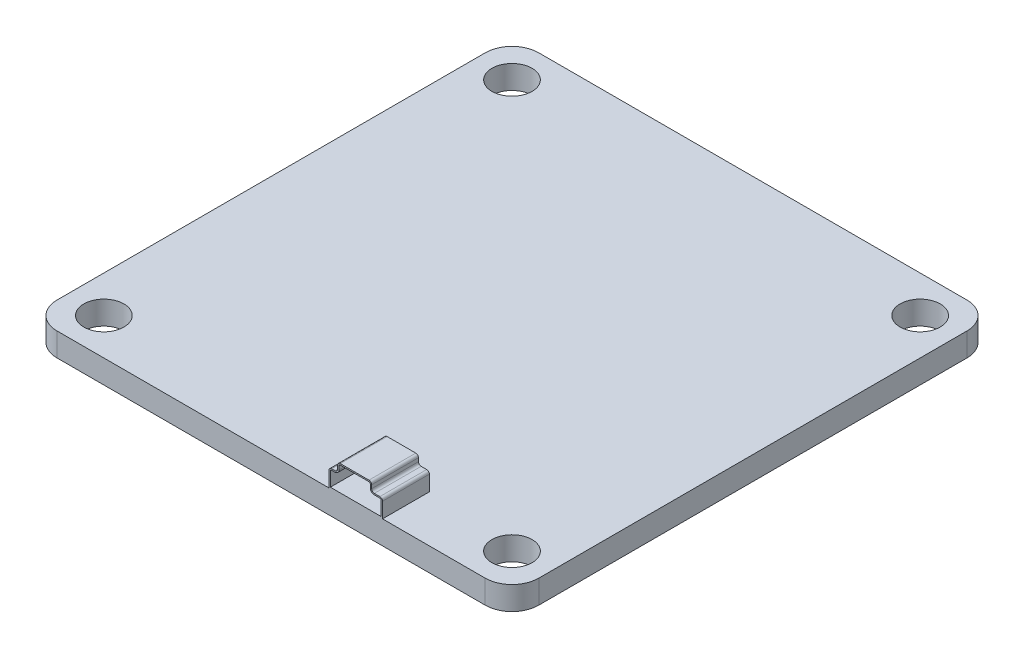
SolidWorks part; units mm, degrees
ref_plane "Front Plane" through (0, 0, 0) normal (0, 0, 1) x (1, 0, 0)
ref_plane "Top Plane" through (0, 0, 0) normal (0, 1, 0) x (1, 0, 0)
ref_plane "Right Plane" through (0, 0, 0) normal (1, 0, 0) x (0, 0, -1)
sketch "Sketch1" plane through (0, 0, 0) normal (0, 1, 0) x (1, 0, 0)
  line L1 (16, -18) -> (-16, -18)
  line L2 (18, -16) -> (18, 16)
  line L3 (16, 18) -> (-16, 18)
  line L4 (-18, -16) -> (-18, 16)
  line L5 (18, -18) -> (-18, 18) construction
  line L6 (18, 18) -> (-18, -18) construction
  line L7 (15.25, -15.25) -> (-15.25, -15.25) construction
  line L8 (15.25, -15.25) -> (15.25, 15.25) construction
  line L9 (15.25, 15.25) -> (-15.25, 15.25) construction
  line L10 (-15.25, -15.25) -> (-15.25, 15.25) construction
  line L11 (15.25, -15.25) -> (-15.25, 15.25) construction
  line L12 (15.25, 15.25) -> (-15.25, -15.25) construction
  circle A0 centre (-15.25, 15.25) radius 1.5
  circle A1 centre (15.25, 15.25) radius 1.5
  circle A2 centre (15.25, -15.25) radius 1.5
  circle A3 centre (-15.25, -15.25) radius 1.5
  arc A4 (-16, -18) -> (-18, -16) centre (-16, -16) cw
  arc A5 (16, -18) -> (18, -16) centre (16, -16) ccw
  arc A6 (18, 16) -> (16, 18) centre (16, 16) ccw
  arc A7 (-16, 18) -> (-18, 16) centre (-16, 16) ccw
  point P0 (0, 0)
  point P6 (0, 0)
  dimension "D4" = 3
  dimension "D5" = 2
  dimension "D1" = 36
  dimension "D2" = 36
  dimension "D3" = 30.5
extrude "Boss-Extrude1" add sketch "Sketch1" along normal blind 1.75
sketch "Sketch2" plane through (0, 0, 18) normal (0, 0, 1) x (1, 0, 0)
  line L0 (-16, 1.75) -> (16, 1.75) construction
  line L1 (4.3259, 1.75) -> (8.3259, 1.75)
  line L2 (4.3259, 1.75) -> (4.3259, 2.8932)
  line L3 (5.1702, 3.75) -> (7.3106, 3.75)
  line L4 (8.3259, 1.75) -> (8.3259, 2.8932)
  line L5 (4.9702, 3.55) -> (4.9702, 3.2932)
  line L6 (4.7702, 3.0932) -> (4.5259, 3.0932)
  line L7 (7.5106, 3.55) -> (7.5106, 3.2932)
  line L8 (7.7106, 3.0932) -> (8.1259, 3.0932)
  line L9 (4.4259, 1.85) -> (8.2259, 1.85)
  line L10 (8.2259, 1.85) -> (8.2259, 2.8932)
  line L11 (7.7106, 2.9932) -> (8.1259, 2.9932)
  line L12 (7.4106, 3.55) -> (7.4106, 3.2932)
  line L13 (5.1702, 3.65) -> (7.3106, 3.65)
  line L14 (5.0702, 3.55) -> (5.0702, 3.2932)
  line L15 (4.7702, 2.9932) -> (4.5259, 2.9932)
  line L16 (4.4259, 1.85) -> (4.4259, 2.8932)
  arc A0 (8.1259, 3.0932) -> (8.3259, 2.8932) centre (8.1259, 2.8932) cw
  arc A1 (7.5106, 3.2932) -> (7.7106, 3.0932) centre (7.7106, 3.2932) ccw
  arc A2 (7.5106, 3.55) -> (7.3106, 3.75) centre (7.3106, 3.55) ccw
  arc A3 (4.9702, 3.55) -> (5.1702, 3.75) centre (5.1702, 3.55) cw
  arc A4 (4.9702, 3.2932) -> (4.7702, 3.0932) centre (4.7702, 3.2932) cw
  arc A5 (4.5259, 3.0932) -> (4.3259, 2.8932) centre (4.5259, 2.8932) ccw
  arc A6 (8.1259, 2.9932) -> (8.2259, 2.8932) centre (8.1259, 2.8932) cw
  arc A7 (7.4106, 3.2932) -> (7.7106, 2.9932) centre (7.7106, 3.2932) ccw
  arc A8 (7.4106, 3.55) -> (7.3106, 3.65) centre (7.3106, 3.55) ccw
  arc A9 (5.0702, 3.55) -> (5.1702, 3.65) centre (5.1702, 3.55) cw
  arc A10 (5.0702, 3.2932) -> (4.7702, 2.9932) centre (4.7702, 3.2932) cw
  arc A11 (4.5259, 2.9932) -> (4.4259, 2.8932) centre (4.5259, 2.8932) ccw
  dimension "D1" = 0.2
  dimension "D2" = 0.1
extrude "Boss-Extrude2" add sketch "Sketch2" against normal blind 3
sketch "Sketch3" plane through (0, 0, 15) normal (0, 0, -1) x (-1, 0, 0)
  line L8 (-4.3259, 1.75) -> (-4.3259, 2.8932)
  line L9 (-4.5259, 3.0932) -> (-4.7702, 3.0932)
  line L10 (-4.9702, 3.2932) -> (-4.9702, 3.55)
  line L11 (-5.1702, 3.75) -> (-7.3106, 3.75)
  line L12 (-7.5106, 3.55) -> (-7.5106, 3.2932)
  line L13 (-7.7106, 3.0932) -> (-8.1259, 3.0932)
  line L14 (-8.3259, 2.8932) -> (-8.3259, 1.75)
  line L15 (-8.3259, 1.75) -> (-4.3259, 1.75)
  line L16 (-4.3259, 1.75) -> (-4.3259, 2.8932)
  line L17 (-4.5259, 3.0932) -> (-4.7702, 3.0932)
  line L18 (-4.9702, 3.2932) -> (-4.9702, 3.55)
  line L19 (-5.1702, 3.75) -> (-7.3106, 3.75)
  line L20 (-7.5106, 3.55) -> (-7.5106, 3.2932)
  line L21 (-7.7106, 3.0932) -> (-8.1259, 3.0932)
  line L22 (-8.3259, 2.8932) -> (-8.3259, 1.75)
  line L23 (-8.3259, 1.75) -> (-4.3259, 1.75)
  arc A6 (-4.3259, 2.8932) -> (-4.5259, 3.0932) centre (-4.5259, 2.8932) ccw
  arc A7 (-4.9702, 3.2932) -> (-4.7702, 3.0932) centre (-4.7702, 3.2932) ccw
  arc A8 (-4.9702, 3.55) -> (-5.1702, 3.75) centre (-5.1702, 3.55) ccw
  arc A9 (-7.3106, 3.75) -> (-7.5106, 3.55) centre (-7.3106, 3.55) ccw
  arc A10 (-7.7106, 3.0932) -> (-7.5106, 3.2932) centre (-7.7106, 3.2932) ccw
  arc A11 (-8.1259, 3.0932) -> (-8.3259, 2.8932) centre (-8.1259, 2.8932) ccw
  arc A12 (-4.3259, 2.8932) -> (-4.5259, 3.0932) centre (-4.5259, 2.8932) ccw
  arc A13 (-4.9702, 3.2932) -> (-4.7702, 3.0932) centre (-4.7702, 3.2932) ccw
  arc A14 (-4.9702, 3.55) -> (-5.1702, 3.75) centre (-5.1702, 3.55) ccw
  arc A15 (-7.3106, 3.75) -> (-7.5106, 3.55) centre (-7.3106, 3.55) ccw
  arc A16 (-7.7106, 3.0932) -> (-7.5106, 3.2932) centre (-7.7106, 3.2932) ccw
  arc A17 (-8.1259, 3.0932) -> (-8.3259, 2.8932) centre (-8.1259, 2.8932) ccw
  dimension "D1" = 0
extrude "Boss-Extrude3" add sketch "Sketch3" along normal blind 0.5
sketch "Sketch4" plane through (0, 0, 14.5) normal (0, 0, -1) x (-1, 0, 0)
  line L0 (-8.3259, 2.8932) -> (-8.3259, 1.75) construction
  circle A0 centre (-7.3259, 2.8178) radius 0.25
  circle A1 centre (-6.3259, 2.8178) radius 0.25
  circle A2 centre (-5.3259, 2.8178) radius 0.25
  dimension "D1" = 0.5
  dimension "D2" = 1
  dimension "D3" = 1
  dimension "D4" = 2
extrude "Cut-Extrude1" cut sketch "Sketch4" against normal up to next
